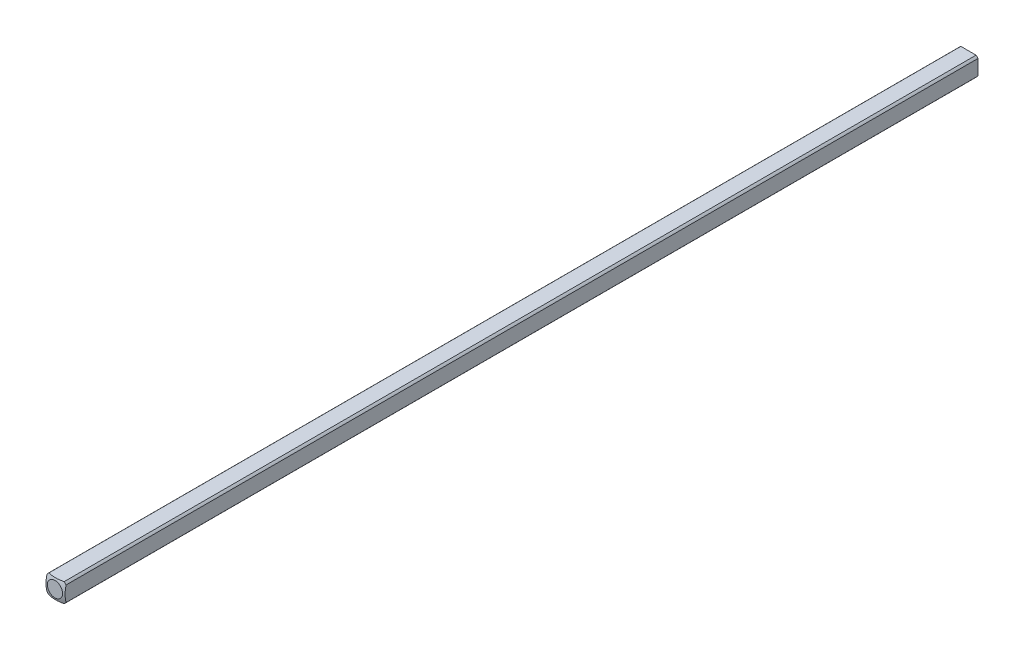
SolidWorks part; units mm, degrees
material "Custom Plastic"
ref_plane "Front Plane" through (0, 0, 0) normal (0, 0, 1) x (1, 0, 0)
ref_plane "Top Plane" through (0, 0, 0) normal (0, 1, 0) x (1, 0, 0)
ref_plane "Right Plane" through (0, 0, 0) normal (1, 0, 0) x (0, 0, -1)
sketch "Sketch1" plane through (0, 0, 0) normal (0, 0, 1) x (1, 0, 0)
  line L0 (-1.5875, -1.5875) -> (1.5875, 1.5875) construction
  line L1 (-1.5875, -1.5875) -> (1.5875, -1.5875)
  line L2 (-1.5875, -1.5875) -> (-1.5875, 1.5875)
  line L3 (-1.5875, 1.5875) -> (1.5875, 1.5875)
  line L4 (1.5875, -1.5875) -> (1.5875, 1.5875)
  dimension "D1" = 3.175
extrude "Boss-Extrude1" add sketch "Sketch1" along normal blind 152.4
sketch "Sketch2" plane through (0, 0, 0) normal (0, 0, -1) x (-1, 0, 0)
  circle A0 centre (0, 0) radius 2.032
  dimension "D1" = 4.064
extrude "Cut-Extrude1" cut sketch "Sketch2" against normal through all flip side to cut
ref_axis "Axis1" through (0, 0, 152.4) along (0, 0, -1)
sketch "Sketch3" plane through (0, 0, 0) normal (0, 1, 0) x (1, 0, 0)
  line L1 (-5.0537, -4.4027) -> (-5.0537, 5.7405)
  line L2 (-5.0537, 5.7405) -> (0, 5.7405)
  line L5 (0, -152.4) -> (0, 0) construction
  line L8 (0, 0.1609) -> (0, 5.7405)
  arc A0 (-5.0537, -4.4027) -> (0, 0.1609) centre (0, -4.9191) cw
  dimension "D1" = 5.08
revolve "Cut-Revolve1" cut sketch "Sketch3" angle 360 about axis through (0, 0, 152.4) along (0, 0, -1)
mirror "Mirror1" about plane through (0, 0, 152.4) normal (0, 0, -1) of bodies 103
sketch "Sketch4" plane through (1.5875, 0, 0) normal (1, 0, 0) x (0, 0, -1)
  line L1 (-0.2632, -1.5875) -> (-152.6632, -1.5875)
  line L2 (-0.2632, 1.5875) -> (-152.6632, 1.5875)
  line L3 (-152.6632, -1.5875) -> (-152.6632, 1.5875)
  line L16 (-0.2632, 1.5875) -> (-0.2632, -1.5875)
  dimension "D1" = 152.4
extrude "Cut-Extrude3" cut sketch "Sketch4" against normal through all
